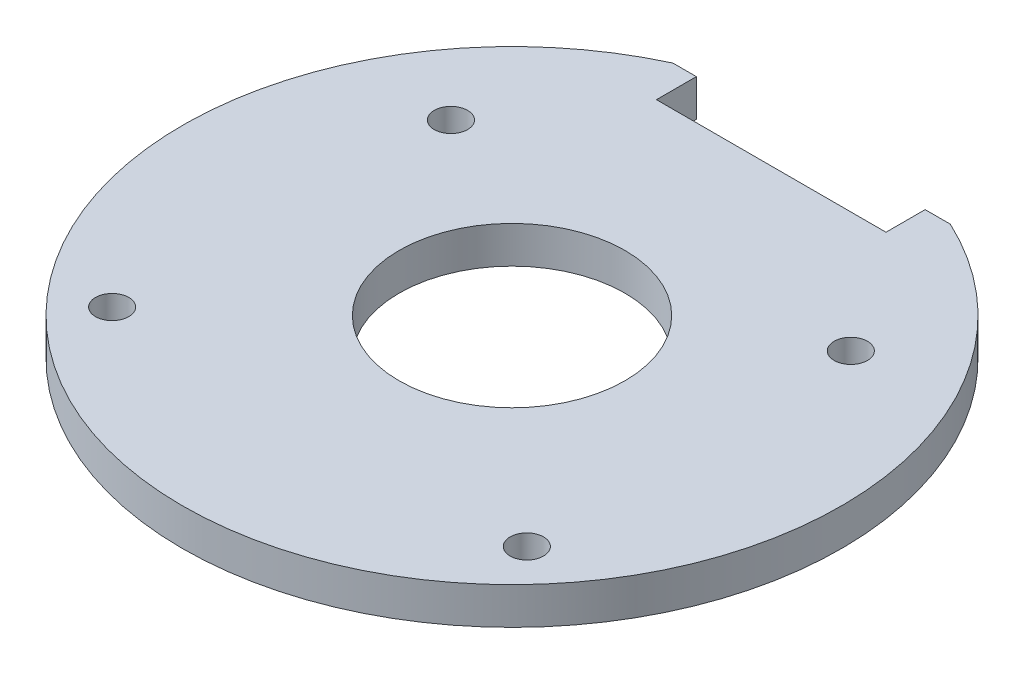
SolidWorks part; units mm, degrees
ref_plane "Спереди" through (0, 0, 0) normal (0, 0, 1) x (1, 0, 0)
ref_plane "Сверху" through (0, 0, 0) normal (0, 1, 0) x (1, 0, 0)
ref_plane "Справа" through (0, 0, 0) normal (1, 0, 0) x (0, 0, -1)
sketch "Эскиз2" plane through (0, 0, 0) normal (0, 1, 0) x (1, 0, 0)
  line L0 (-65, -26) -> (65, -26) construction
  line L1 (-65, 18.75) -> (65, 18.75) construction
  line L2 (-27, 50) -> (-27, -50) construction
  line L3 (27, 50) -> (27, -50) construction
  line L5 (-15.5, 35) -> (15.5, 35)
  line L7 (-15.5, 40.3935) -> (-15.5, 35)
  line L8 (15.5, 40.2863) -> (15.5, 35)
  line L9 (15.5, 40.2863) -> (18.9014, 40.2863)
  line L10 (-15.5, 40.3935) -> (-18.6713, 40.3935)
  line L11 (-28, -10.8076) -> (-28, -38.8076) construction
  line L12 (0, 51.1089) -> (0, -51.8899) construction
  line L13 (28, -10.8076) -> (28, -38.8076) construction
  arc A0 (-18.6713, 40.3935) -> (18.9014, 40.2863) centre (0, 0) ccw
  circle A2 centre (0, 0) radius 15.25
  circle A3 centre (-27, 18.75) radius 2.25
  circle A4 centre (27, 18.75) radius 2.25
  circle A5 centre (28, -26) radius 2.25
  circle A6 centre (-28, -26) radius 2.25
extrude "Бобышка-Вытянуть1" add sketch "Эскиз2" along normal blind 5
sketch "Эскиз3" plane through (0, 5, 0) normal (0, 1, 0) x (1, 0, 0)
  line L0 (324.9693, 1032.1436) -> (1864.8984, 1046.9263) construction
